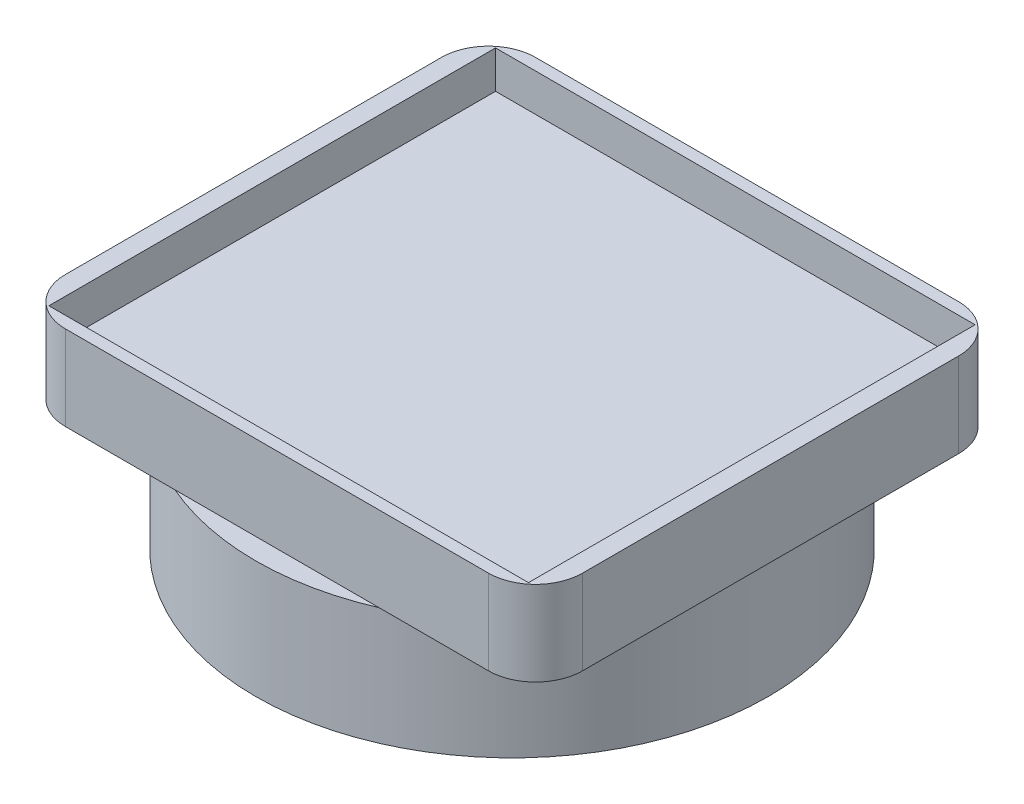
SolidWorks part; units mm, degrees
material "201.0-T43 Insulated Mold Casting (SS)"
ref_plane "Front Plane" through (0, 0, 0) normal (0, 0, 1) x (1, 0, 0)
ref_plane "Top Plane" through (0, 0, 0) normal (0, 1, 0) x (1, 0, 0)
ref_plane "Right Plane" through (0, 0, 0) normal (1, 0, 0) x (0, 0, -1)
sketch "Sketch1" plane through (0, 0, 0) normal (0, 1, 0) x (1, 0, 0)
  line L1 (-12.954, 12.065) -> (12.954, 12.065)
  line L2 (-12.954, 12.065) -> (-12.954, -12.065)
  line L3 (-12.954, -12.065) -> (12.954, -12.065)
  line L4 (12.954, 12.065) -> (12.954, -12.065)
  line L5 (-12.954, 12.065) -> (12.954, -12.065) construction
  line L6 (-12.954, -12.065) -> (12.954, 12.065) construction
  line L7 (-13.97, 12.7) -> (13.97, 12.7)
  line L8 (-13.97, 12.7) -> (-13.97, -12.7)
  line L9 (-13.97, -12.7) -> (13.97, -12.7)
  line L10 (13.97, 12.7) -> (13.97, -12.7)
  line L11 (-13.97, 12.7) -> (13.97, -12.7) construction
  line L12 (-13.97, -12.7) -> (13.97, 12.7) construction
  point P0 (0, 0)
  point P5 (0, 0)
  dimension "D1" = 25.908
  dimension "D2" = 27.94
  dimension "D3" = 24.13
  dimension "D4" = 25.4
extrude "Boss-Extrude1" add sketch "Sketch1" along normal blind 2.032
sketch "Sketch2" plane through (0, 0, 0) normal (0, 1, 0) x (1, 0, 0)
  line L1 (13.97, 12.7) -> (-13.97, 12.7)
  line L2 (13.97, 12.7) -> (13.97, -12.7)
  line L3 (13.97, -12.7) -> (-13.97, -12.7)
  line L4 (-13.97, 12.7) -> (-13.97, -12.7)
  line L5 (13.97, 12.7) -> (-13.97, -12.7) construction
  line L6 (13.97, -12.7) -> (-13.97, 12.7) construction
  point P0 (0, 0)
extrude "Boss-Extrude2" add sketch "Sketch2" against normal blind 2.54
sketch "Sketch3" plane through (0, -2.54, 0) normal (0, -1, 0) x (1, 0, 0)
  circle A0 centre (0, 0) radius 13.843
  dimension "D1" = 27.686
extrude "Boss-Extrude3" add sketch "Sketch3" along normal blind 6.35
fillet "Fillet1" radius 2.54 4 edges at (-13.97, -0.254, -12.7) (-13.97, -0.254, 12.7) (13.97, -0.254, 12.7) (13.97, -0.254, -12.7)
